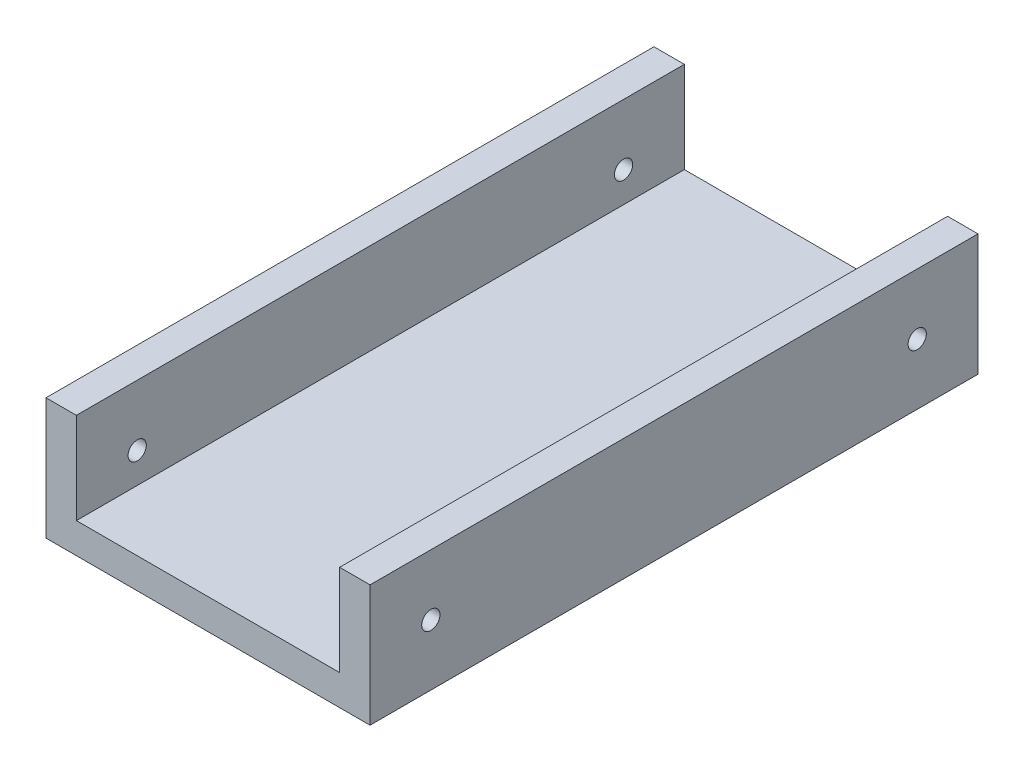
SolidWorks part; units mm, degrees
ref_plane "Plan de face" through (0, 0, 0) normal (0, 0, 1) x (1, 0, 0)
ref_plane "Plan de dessus" through (0, 0, 0) normal (0, 1, 0) x (1, 0, 0)
ref_plane "Plan de droite" through (0, 0, 0) normal (1, 0, 0) x (0, 0, -1)
sketch "Esquisse1" plane through (0, 0, 0) normal (0, 1, 0) x (1, 0, 0)
  line L1 (0, 0) -> (53.3, 0)
  line L2 (0, 0) -> (0, -100)
  line L3 (0, -100) -> (53.3, -100)
  line L4 (53.3, 0) -> (53.3, -100)
  dimension "D1" = 53.3
  dimension "D2" = 100
extrude "Boss.-Extru.1" add sketch "Esquisse1" along normal blind 20
sketch "Esquisse2" plane through (0, 20, 0) normal (0, 1, 0) x (1, 0, 0)
  line L0 (0, 0) -> (0, -100) construction
  line L1 (5, 0) -> (48.3, 0)
  line L2 (5, 0) -> (5, -100)
  line L3 (5, -100) -> (48.3, -100)
  line L4 (48.3, 0) -> (48.3, -100)
  line L5 (53.3, -100) -> (53.3, 0) construction
  line L6 (0, -100) -> (53.3, -100) construction
  line L7 (53.3, 0) -> (0, 0) construction
  dimension "D1" = 5
  dimension "D2" = 5
  dimension "D3" = 0
  dimension "D4" = 0
extrude "Enlèv. mat.-Extru.1" cut sketch "Esquisse2" against normal blind 15
sketch "Esquisse3" plane through (53.3, 0, 0) normal (1, 0, 0) x (0, 0, -1)
  line L0 (-100, 20) -> (-100, 0) construction
  line L1 (-100, 20) -> (0, 20) construction
  line L2 (-50, 20) -> (-50, 0) construction
  circle A0 centre (-90, 10) radius 1.5
  circle A1 centre (-10, 10) radius 1.5
  dimension "D3" = 3
  dimension "D1" = 10
  dimension "D2" = 10
extrude "Enlèv. mat.-Extru.2" cut sketch "Esquisse3" against normal through all
